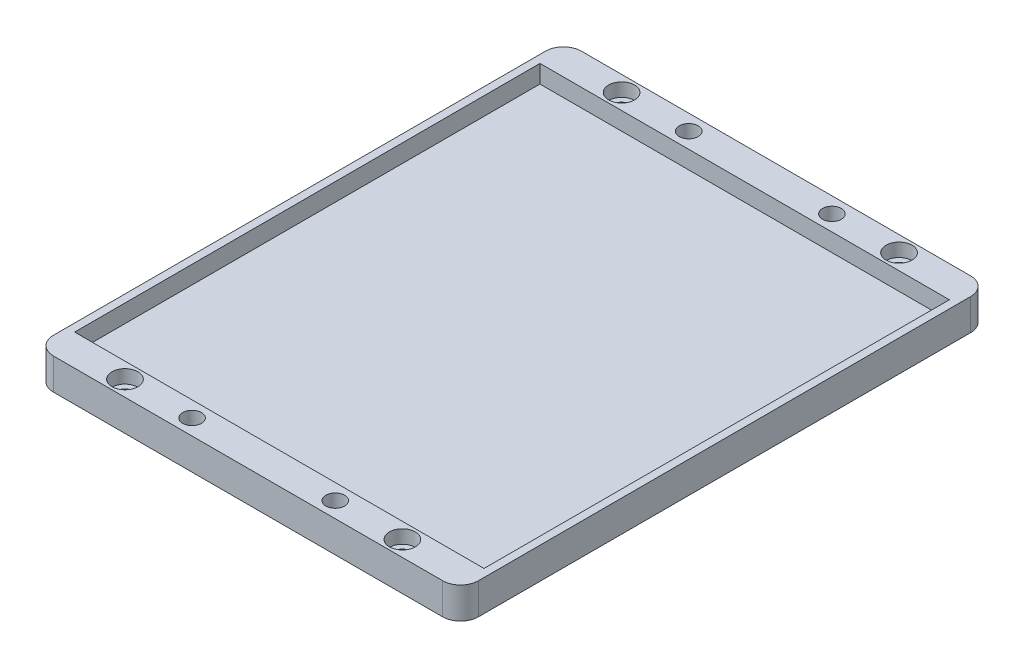
SolidWorks part; units mm, degrees
ref_plane "Płaszczyzna przednia" through (0, 0, 0) normal (0, 0, 1) x (1, 0, 0)
ref_plane "Płaszczyzna górna" through (0, 0, 0) normal (0, 1, 0) x (1, 0, 0)
ref_plane "Płaszczyzna prawa" through (0, 0, 0) normal (1, 0, 0) x (0, 0, -1)
sketch "Szkic1" plane through (0, 0, 0) normal (0, 1, 0) x (1, 0, 0)
  line L1 (-47.5, 59) -> (47.5, 59)
  line L2 (-47.5, 59) -> (-47.5, -59)
  line L3 (-47.5, -59) -> (47.5, -59)
  line L4 (47.5, 59) -> (47.5, -59)
  line L5 (-47.5, 59) -> (47.5, -59) construction
  line L6 (-47.5, -59) -> (47.5, 59) construction
  point P0 (0, 0)
  dimension "D1" = 118
  dimension "D2" = 95
extrude "Dodanie-wyciągnięcie1" add sketch "Szkic1" along normal blind 7
sketch "Szkic2" plane through (0, 7, 0) normal (0, 1, 0) x (1, 0, 0)
  line L1 (-45.75, -52) -> (45.75, -52)
  line L2 (-45.75, -52) -> (-45.75, 52)
  line L3 (-45.75, 52) -> (45.75, 52)
  line L4 (45.75, -52) -> (45.75, 52)
  line L5 (-45.75, -52) -> (45.75, 52) construction
  line L6 (-45.75, 52) -> (45.75, -52) construction
  point P0 (0, 0)
  dimension "D1" = 104
  dimension "D2" = 91.5
extrude "Wytnij-wyciągnięcie1" cut sketch "Szkic2" against normal blind 4
sketch "Szkic4" plane through (0, 7, 0) normal (0, 1, 0) x (1, 0, 0)
  line L0 (0, -66) -> (0, -52) construction
  line L1 (-31, -55.5) -> (31, -55.5) construction
  line L3 (-3.85, 0) -> (3.85, 0) construction
  line L4 (-45.75, -52) -> (45.75, -52) construction
  line L5 (-47.5, -59) -> (47.5, -59) construction
  circle A0 centre (31, -55.5) radius 1.6
  circle A1 centre (-31, -55.5) radius 1.6
  circle A2 centre (31, 55.5) radius 1.6
  circle A3 centre (-31, 55.5) radius 1.6
  point P0 (0, -56.9358)
  point P5 (0, -55.5)
  point P9 (0, -59)
  dimension "D3" = 3.2
  dimension "D4" = 3.2
  dimension "D1" = 3.5
  dimension "D2" = 62
  dimension "D5" = 7
extrude "Wytnij-wyciągnięcie3" cut sketch "Szkic4" against normal through all
fillet "Zaokrąglenie1" radius 4 4 edges at (47.5, 3.5, -59) (-47.5, 3.5, -59) (47.5, 3.5, 59) (-47.5, 3.5, 59)
sketch "Szkic5" plane through (0, 7, 0) normal (0, 1, 0) x (1, 0, 0)
  line L0 (-3.85, 0) -> (3.85, 0) construction
  line L1 (0, -3.85) -> (0, 3.85) construction
  circle A0 centre (-31, -55.5) radius 2.9
  circle A1 centre (-31, -55.5) radius 1.6 construction
  circle A2 centre (-31, 55.5) radius 2.9
  circle A3 centre (31, -55.5) radius 2.9
  circle A4 centre (31, 55.5) radius 2.9
  dimension "D1" = 5.8
extrude "Wytnij-wyciągnięcie4" cut sketch "Szkic5" against normal blind 3
sketch "Szkic6" plane through (0, 7, 0) normal (0, 1, 0) x (1, 0, 0)
  line L0 (-43.5, -59) -> (43.5, -59) construction
  line L5 (-3.85, 0) -> (3.85, 0) construction
  line L6 (0, -3.85) -> (0, 3.85) construction
  circle A0 centre (-16, -55.5) radius 2.1
  circle A1 centre (-16, 55.5) radius 2.1
  circle A2 centre (16, 55.5) radius 2.1
  circle A3 centre (16, -55.5) radius 2.1
  dimension "D3" = 4.2
  dimension "D1" = 3.5
  dimension "D2" = 16
extrude "Wytnij-wyciągnięcie5" cut sketch "Szkic6" against normal blind 6
